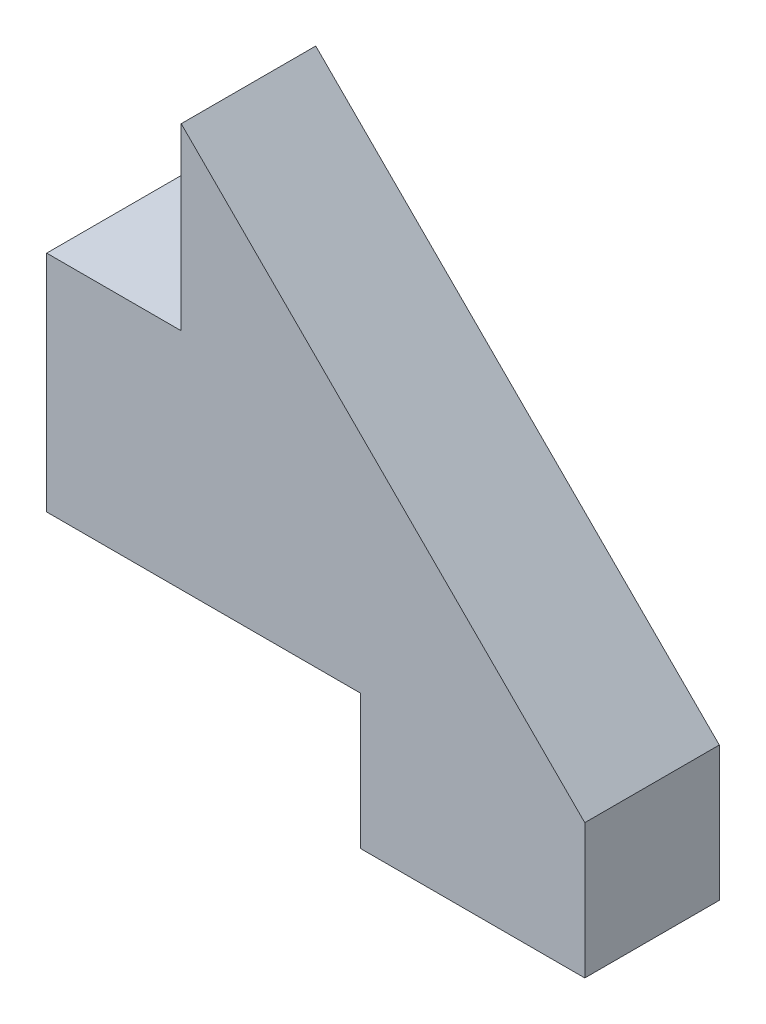
SolidWorks part; units mm, degrees
ref_plane "Front Plane" through (0, 0, 0) normal (0, 0, 1) x (1, 0, 0)
ref_plane "Top Plane" through (0, 0, 0) normal (0, 1, 0) x (1, 0, 0)
ref_plane "Right Plane" through (0, 0, 0) normal (1, 0, 0) x (0, 0, -1)
sketch "Sketch1" plane through (0, 0, 0) normal (0, 0, 1) x (1, 0, 0)
  line L0 (0, 0) -> (0, 10)
  line L1 (6, 18) -> (24, 0)
  line L3 (24, 0) -> (24, -6)
  line L6 (0, 0) -> (14, 0)
  line L7 (14, -6) -> (14, 0)
  line L8 (0, 10) -> (6, 10)
  line L11 (6, 10) -> (6, 18)
  line L12 (24, -6) -> (14, -6)
  dimension "D1" = 10
  dimension "D2" = 6
  dimension "D3" = 8
  dimension "D4" = 14
  dimension "D5" = 6
  dimension "D6" = 10
  dimension "D7" = 6
extrude "Boss-Extrude1" add sketch "Sketch1" along normal blind 6
